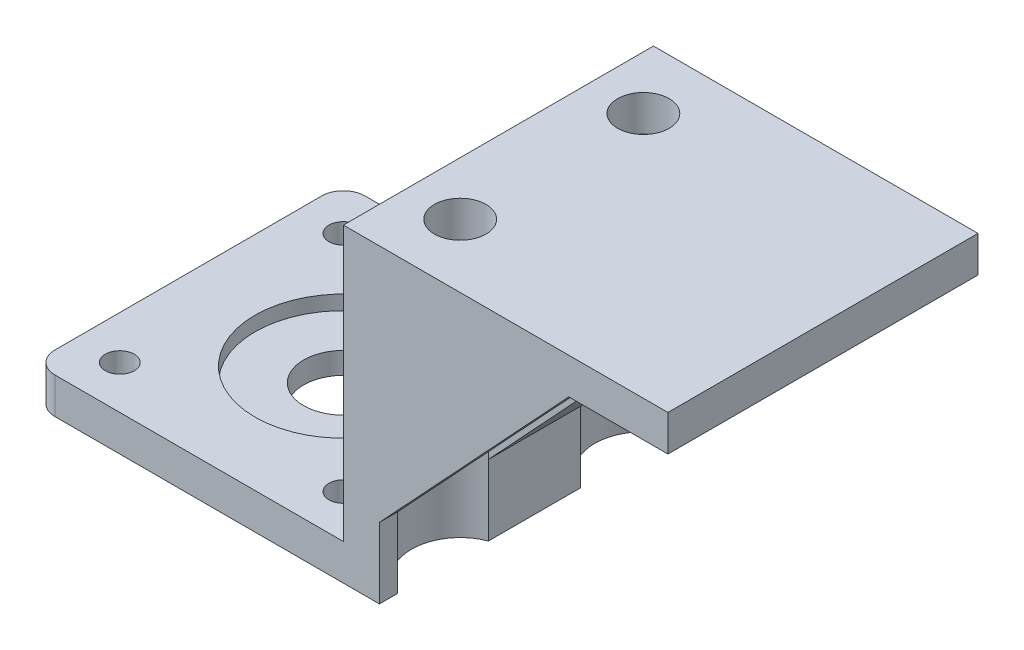
SolidWorks part; units mm, degrees
material "ABS"
ref_plane "Front Plane" through (0, 0, 0) normal (0, 0, 1) x (1, 0, 0)
ref_plane "Top Plane" through (0, 0, 0) normal (0, 1, 0) x (1, 0, 0)
ref_plane "Right Plane" through (0, 0, 0) normal (1, 0, 0) x (0, 0, -1)
sketch "Sketch1" plane through (0, 0, 0) normal (0, 1, 0) x (1, 0, 0)
  line L1 (0, -0.5475) -> (43, -0.5475)
  line L2 (0, -0.5475) -> (0, -43.5475)
  line L3 (0, -43.5475) -> (43, -43.5475)
  line L4 (43, -0.5475) -> (43, -43.5475)
  dimension "D1" = 43
  dimension "D2" = 43
extrude "Boss-Extrude1" add sketch "Sketch1" along normal blind 5
fillet "Fillet1" radius 3 2 edges at (0, 2.5, 0.5475) (0, 2.5, 43.5475)
sketch "Sketch2" plane through (0, 5, 0) normal (0, 1, 0) x (1, 0, 0)
  line L0 (0, -6.5475) -> (43, -6.5475) construction
  line L1 (0, -3.5475) -> (0, -40.5475) construction
  line L2 (43, -43.5475) -> (43, -0.5475) construction
  line L3 (0, -37.5475) -> (43, -37.5475) construction
  line L4 (6, -6.5475) -> (6, -31.6676) construction
  line L5 (37, -6.5475) -> (37, -31.6676) construction
  line L6 (3, -43.5475) -> (43, -43.5475) construction
  circle A0 centre (6, -37.5475) radius 0.9759
  circle A1 centre (37, -37.5475) radius 1.1565
  circle A2 centre (37, -6.5475) radius 0.9282
  circle A3 centre (6, -6.5475) radius 1.4945
  dimension "D1" = 31
  dimension "D2" = 31
  dimension "D3" = 6
  dimension "D4" = 6
  dimension "D5" = 6
hole_wizard "Ø4.0mm Dowel Hole1" positions "Sketch3" profile "Sketch4" hole size "Ø4.0" standard "ANSI Metric"
sketch "Sketch3" plane through (0, 5, 0) normal (0, 1, 0) x (1, 0, 0)
  point P0 (6, -6.5475)
  point P3 (37, -6.5475)
  point P6 (37, -37.5475)
  point P9 (6, -37.5475)
sketch "Sketch4" plane through (6, 5, 6.5475) normal (1, 0, 0) x (0, 0, 1)
  line L0 (0, 0) -> (0, 11.2017)
  line L1 (0, 11.2017) -> (2, 10)
  line L2 (2, 10) -> (2, 0)
  line L5 (2, 0) -> (0, 0)
  line L10 (0, 11.2017) -> (-2, 10) construction
  line L11 (0, -6.35) -> (0, 107.95) construction
  dimension "Hole Dia." = 4
  dimension "Hole Depth" = 10
  dimension "Drill Angle" = 118
sketch "Sketch5" plane through (0, 5, 0) normal (0, 1, 0) x (1, 0, 0)
  line L0 (43, -43.5475) -> (0.8787, -1.4262) construction
  arc A0 (3, -0.5475) -> (0, -3.5475) centre (3, -3.5475) ccw construction
  circle A1 centre (21.9393, -22.4868) radius 5.5
  dimension "D1" = 11
extrude "Cut-Extrude1" cut sketch "Sketch5" against normal blind 5
sketch "Sketch6" plane through (0, 5, 0) normal (0, 1, 0) x (1, 0, 0)
  line L1 (43, -43.5475) -> (48, -43.5475)
  line L2 (43, -43.5475) -> (43, -0.5475)
  line L3 (43, -0.5475) -> (48, -0.5475)
  line L4 (48, -43.5475) -> (48, -0.5475)
  dimension "D1" = 5
extrude "Boss-Extrude2" add sketch "Sketch6" along normal blind 38 and the other way blind 5 contours L4 L3 L2 L1
sketch "Sketch10" plane through (0, 5, 0) normal (0, 1, 0) x (1, 0, 0)
  circle A0 centre (21.9393, -22.4868) radius 12.25
  dimension "D1" = 24.5
sketch "Sketch11" plane through (0, 0, 0) normal (0, -1, 0) x (1, 0, 0)
  circle A0 centre (21.9393, 22.4868) radius 12.25
extrude "Cut-Extrude4" cut sketch "Sketch11" along normal blind 2 from surface at -5 starting at face at (21.9393, 5, 27.9868)
sketch "Sketch12" plane through (48, 0, 0) normal (1, 0, 0) x (0, 0, -1)
  line L0 (-0.5475, 0) -> (-0.5475, 43) construction
  line L1 (-0.5475, 38) -> (-43.5475, 38)
  line L2 (-0.5475, 38) -> (-0.5475, 43)
  line L3 (-0.5475, 43) -> (-43.5475, 43)
  line L4 (-43.5475, 38) -> (-43.5475, 43)
  dimension "D1" = 5
extrude "Boss-Extrude3" add sketch "Sketch12" along normal blind 40
sketch "Sketch13" plane through (0, 38, 0) normal (0, -1, 0) x (-1, 0, 0)
  line L0 (-50.4, -9.3475) -> (-50.4, -34.7475) construction
  line L4 (-88, -22.0475) -> (-48, -22.0475) construction
  line L5 (-88, -43.5475) -> (-88, -0.5475) construction
  line L6 (-48, -43.5475) -> (-48, -0.5475) construction
  line L7 (-43, -43.5475) -> (-43, -0.5475) construction
  circle A0 centre (-50.4, -9.3475) radius 3.5719
  circle A1 centre (-50.4, -34.7475) radius 3.5719
  point P2 (-50.4, -22.0475)
  dimension "D2" = 7.1437
  dimension "D3" = 7.1437
  dimension "D1" = 7.4
  dimension "D4" = 25.4
extrude "Cut-Extrude5" cut sketch "Sketch13" against normal blind 10
sketch "Sketch15" plane through (0, 38, 0) normal (0, -1, 0) x (1, 0, 0)
  circle A0 centre (50.4, 9.3475) radius 6.75
  circle A1 centre (50.4, 34.7475) radius 6.75
  dimension "D1" = 13.5
  dimension "D2" = 13.5
extrude "Cut-Extrude6" cut sketch "Sketch15" along normal blind 38
sketch "Sketch16" plane through (0, 0, 0.5475) normal (0, 0, -1) x (-1, 0, 0)
  line L2 (-88, 38) -> (-48, 38) construction
  line L5 (-48, 9.8008) -> (-74.2613, 38)
  line L6 (-48, 0) -> (-48, 38) construction
  line L7 (-74.2613, 38) -> (-48, 38)
  line L8 (-48, 9.8008) -> (-48, 38)
extrude "Boss-Extrude4" add sketch "Sketch16" against normal blind 2.5
ref_plane "Plane1" through (0, 0, 22.0475) normal (0, 0, 1) x (1, 0, 0)
pattern_linear "LPattern1" count 3 spacing 20.25 along (0, 0, 1) of "Boss-Extrude4"
sketch "Sketch18" plane through (0, 0, 20.7975) normal (0, 0, -1) x (-1, 0, 0)
  line L0 (-48, 38) -> (-48, 9.8008)
  line L1 (-48, 9.8008) -> (-74.2613, 38)
  line L2 (-74.2613, 38) -> (-48, 38)
extrude "Boss-Extrude5" add sketch "Sketch18" along normal up to vertex (5.1411 mm away) and the other way up to vertex (7.6411 mm away)
sketch "Sketch19" plane through (0, 0, 0) normal (0, -1, 0) x (-1, 0, 0)
  line L0 (-10, -5.5475) -> (-41, -5.5475) construction
  line L1 (-15, 5.8025) -> (-36, 5.8025)
  line L2 (-15, 5.8025) -> (-15, -0.5475)
  line L4 (-36, 5.8025) -> (-36, -0.5475)
  line L5 (-25.5, 5.8025) -> (-25.5, -43.5475) construction
  line L6 (-3, -43.5475) -> (-48, -43.5475) construction
  line L7 (-48, -0.5475) -> (-3, -0.5475) construction
  line L8 (-10, 10.8025) -> (-10, -0.5475)
  line L10 (-41, 10.8025) -> (-41, -0.5475)
  line L11 (-10, 10.8025) -> (-41, 10.8025)
  line L12 (-15, -0.5475) -> (-10, -0.5475)
  line L13 (-36, -0.5475) -> (-41, -0.5475)
  line L14 (-41, 10.8025) -> (-41, -5.5475) construction
  line L15 (-10, 10.8025) -> (-10, -5.5475) construction
  line L16 (-15, -0.5475) -> (-36, -0.5475) construction
  point P17 (-25.5, -43.5475)
  dimension "D1" = 21
  dimension "D2" = 6.35
  dimension "D3" = 5
extrude "Boss-Extrude6" add sketch "Sketch19" against normal up to surface (5 mm away) up to face at (21.9393, 5, 34.7368)
